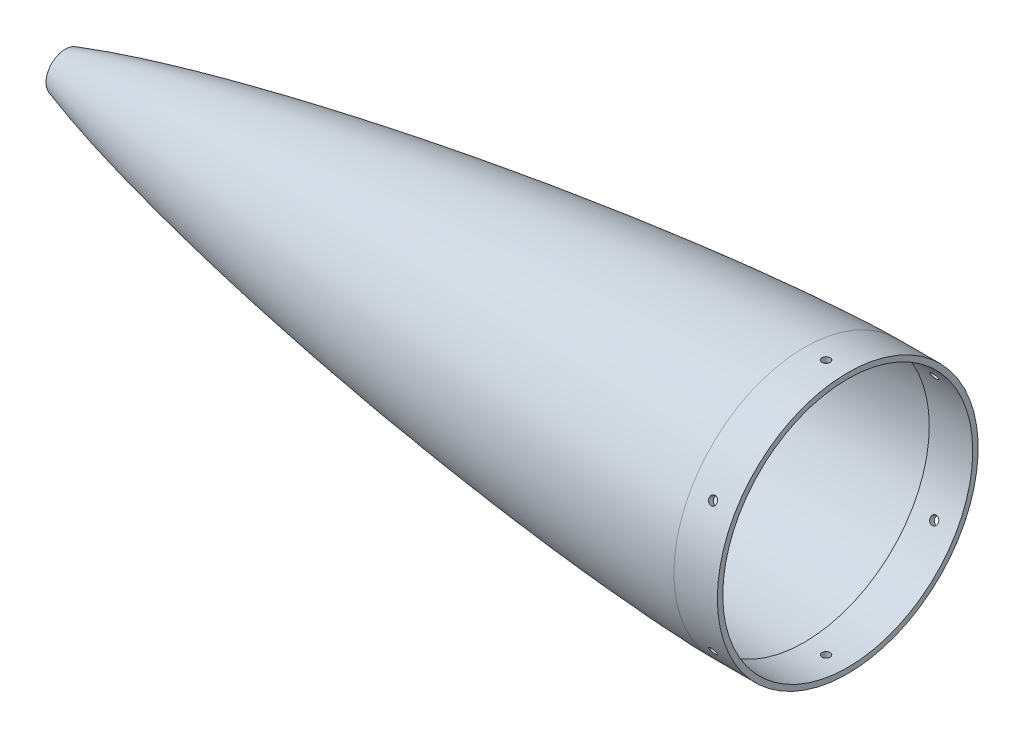
SolidWorks part; units mm, degrees
material "A-Glass Fiber"
ref_plane "Front Plane" through (0, 0, 0) normal (0, 0, 1) x (1, 0, 0)
ref_plane "Top Plane" through (0, 0, 0) normal (0, 1, 0) x (1, 0, 0)
ref_plane "Right Plane" through (0, 0, 0) normal (1, 0, 0) x (0, 0, -1)
sketch "Sketch6" plane through (0, 0, 0) normal (0, 0, 1) x (1, 0, 0)
  line L0 (-61.6447, 0) -> (914.4764, 0) construction
  line L1 (50.8, 22.5304) -> (50.8, 6.35)
  line L2 (50.8, 6.35) -> (53.975, 6.35)
  line L3 (53.975, 6.35) -> (53.975, 20.2276)
  line L4 (914.4, 152.4) -> (965.2, 152.4)
  line L5 (965.2, 152.4) -> (965.2, 149.225)
  line L6 (965.2, 149.225) -> (1066.8, 149.225)
  line L7 (1066.8, 149.225) -> (1066.8, 146.05)
  line L8 (1066.8, 146.05) -> (914.4108, 146.05)
  line L9 (914.4108, 146.05) -> (914.4108, 149.225)
  line L10 (914.4764, 0) -> (914.4764, 254.345) construction
  spline S0 degree 4 poles (0.7109, 0.9249) (0.8194, 1.0297) (1.0401, 1.2349) (1.4358, 1.5745) (2.113, 2.1031) (3.1076, 2.8103) (4.6829, 3.824) (7.1818, 5.2703) (10.3353, 6.9058) (13.9855, 8.6421) (18.4315, 10.6148) (23.2827, 12.6355) (27.8273, 14.4199) (32.0456, 16.0063) (35.3451, 17.212) (37.7085, 18.0607) (40.0869, 18.9004) (42.4489, 19.7217) (44.8547, 20.5452) (47.1736, 21.3287) (50.0431, 22.2836) (52.5896, 23.1187) (57.1138, 24.5817) (62.1376, 26.1632) (68.4729, 28.1134) (76.3898, 30.4748) (85.386, 33.0811) (95.2414, 35.8415) (106.1049, 38.7887) (117.8122, 41.8678) (130.4239, 45.085) (143.9074, 48.4172) (158.286, 51.8608) (172.6821, 55.208) (187.101, 58.4688) (201.5363, 61.648) (215.9891, 64.7518) (234.0733, 68.5424) (255.8026, 72.9566) (281.1895, 77.9247) (306.6148, 82.6926) (328.4324, 86.6462) (350.2681, 90.4977) (372.1212, 94.25) (397.6401, 98.4881) (426.8345, 103.1476) (456.0568, 107.6286) (485.3054, 111.935) (514.5788, 116.0692) (543.8758, 120.0326) (573.1954, 123.8249) (602.5369, 127.4447) (631.8994, 130.8892) (661.2825, 134.1539) (698.0365, 138.0018) (742.1809, 142.23) (786.3738, 145.927) (830.6152, 148.9895) (864.1455, 150.8175) (884.9324, 151.7025) (900.3474, 152.1772) (908.3769, 152.3409) (912.3922, 152.3932) (914.4, 152.4) knots 0 0 0 0 0 0.000648 0.001296 0.002242 0.003694 0.005895 0.00935 0.014656 0.018967 0.023278 0.030267 0.037257 0.039961 0.042665 0.045369 0.048073 0.050777 0.053481 0.056184 0.058888 0.062862 0.066835 0.074782 0.082729 0.090676 0.102753 0.114829 0.126906 0.138983 0.154877 0.170771 0.186664 0.202558 0.218452 0.234346 0.250239 0.266133 0.297921 0.329708 0.361496 0.37739 0.393283 0.425071 0.456858 0.488646 0.520434 0.552221 0.584009 0.615796 0.647584 0.679371 0.711159 0.742946 0.774734 0.838309 0.901884 0.933672 0.965459 0.98273 0.991365 1 1 1 1 1 construction
  spline S1 degree 4 poles (50.8, 22.5304) (51.626, 22.8019) (53.2474, 23.3314) (57.1138, 24.5817) (62.1376, 26.1632) (68.4729, 28.1134) (76.3898, 30.4748) (85.386, 33.0811) (95.2414, 35.8415) (106.1049, 38.7887) (117.8122, 41.8678) (130.4239, 45.085) (143.9074, 48.4172) (158.286, 51.8608) (172.6821, 55.208) (187.101, 58.4688) (201.5363, 61.648) (215.9891, 64.7518) (234.0733, 68.5424) (255.8026, 72.9566) (281.1895, 77.9247) (306.6148, 82.6926) (328.4324, 86.6462) (350.2681, 90.4977) (372.1212, 94.25) (397.6401, 98.4881) (426.8345, 103.1476) (456.0568, 107.6286) (485.3054, 111.935) (514.5788, 116.0692) (543.8758, 120.0326) (573.1954, 123.8249) (602.5369, 127.4447) (631.8994, 130.8892) (661.2825, 134.1539) (698.0365, 138.0018) (742.1809, 142.23) (786.3738, 145.927) (830.6152, 148.9895) (864.1455, 150.8175) (884.9324, 151.7025) (900.3474, 152.1772) (908.3769, 152.3409) (912.3922, 152.3932) (914.4, 152.4) knots 0.058888 0.058888 0.058888 0.058888 0.058888 0.062862 0.066835 0.074782 0.082729 0.090676 0.102753 0.114829 0.126906 0.138983 0.154877 0.170771 0.186664 0.202558 0.218452 0.234346 0.250239 0.266133 0.297921 0.329708 0.361496 0.37739 0.393283 0.425071 0.456858 0.488646 0.520434 0.552221 0.584009 0.615796 0.647584 0.679371 0.711159 0.742946 0.774734 0.838309 0.901884 0.933672 0.965459 0.98273 0.991365 1 1 1 1 1
  spline S2 degree 1 poles (51.7917, 19.5142) (914.4108, 149.225) knots 0 0 1 1 construction
  spline S3 degree 3 poles (51.7917, 19.5142) (52.3018, 19.6819) (53.3014, 20.0091) (54.9287, 20.5374) (56.6361, 21.0877) (58.8672, 21.801) (61.5224, 22.6387) (64.7365, 23.6378) (68.0235, 24.6466) (72.3944, 25.9697) (77.8023, 27.5732) (84.3723, 29.4771) (93.1182, 31.9541) (108.4668, 36.1652) (130.4916, 41.8757) (165.8703, 50.4899) (210.3031, 60.4494) (281.6931, 75.068) (371.3475, 91.3103) (479.375, 108.2298) (569.6849, 120.3768) (642.0768, 128.9125) (696.4384, 134.6926) (750.8635, 139.8007) (796.2675, 143.4252) (832.6178, 145.8603) (859.8907, 147.4162) (882.6287, 148.4363) (898.5341, 148.9465) (907.6277, 149.151) (912.1473, 149.2173) (914.4108, 149.225) knots 0.058888 0.058888 0.058888 0.058888 0.060726 0.062565 0.064403 0.066241 0.069917 0.073593 0.077269 0.080946 0.088298 0.095651 0.103003 0.117708 0.147118 0.176527 0.235347 0.294166 0.411805 0.529444 0.647083 0.705903 0.764722 0.823542 0.882361 0.911771 0.941181 0.97059 0.985295 0.992648 1 1 1 1 only from (53.975, 20.2276) to (914.4108, 149.225)
  dimension "D2" = 3.175
  dimension "D3" = 6.35
  dimension "D4" = 3.175
  dimension "D5" = 101.6
  dimension "D6" = 50.8
  dimension "D7" = 3.175
  dimension "D1" = 3.175
revolve "Revolve1" add sketch "Sketch6" angle 360 about L0
sketch "Sketch7" plane through (965.2, 0, 0) normal (1, 0, 0) x (0, 0, -1)
  circle A0 centre (0, 0) radius 152.4
extrude "Cut-Extrude1" cut sketch "Sketch7" along normal blind 147.3991
ref_plane "Plane2" through (0, 152.4, 0) normal (0, 1, 0) x (1, 0, 0)
sketch "Sketch14" plane through (0, 152.4, 0) normal (0, 1, 0) x (1, 0, 0)
  line L0 (965.2, 0) -> (939.8, 0)
  line L1 (914.4, 0) -> (965.2, 0) construction
  dimension "D1" = 25.4
sketch "Sketch17" plane through (0, 152.4, 0) normal (0, 1, 0) x (1, 0, 0)
  circle A0 centre (939.8, 0) radius 4.7625
extrude "Cut-Extrude4" cut sketch "Sketch17" against normal blind 147.3991
pattern_circular "CirPattern2" count 6 over 360 of "Cut-Extrude4"
